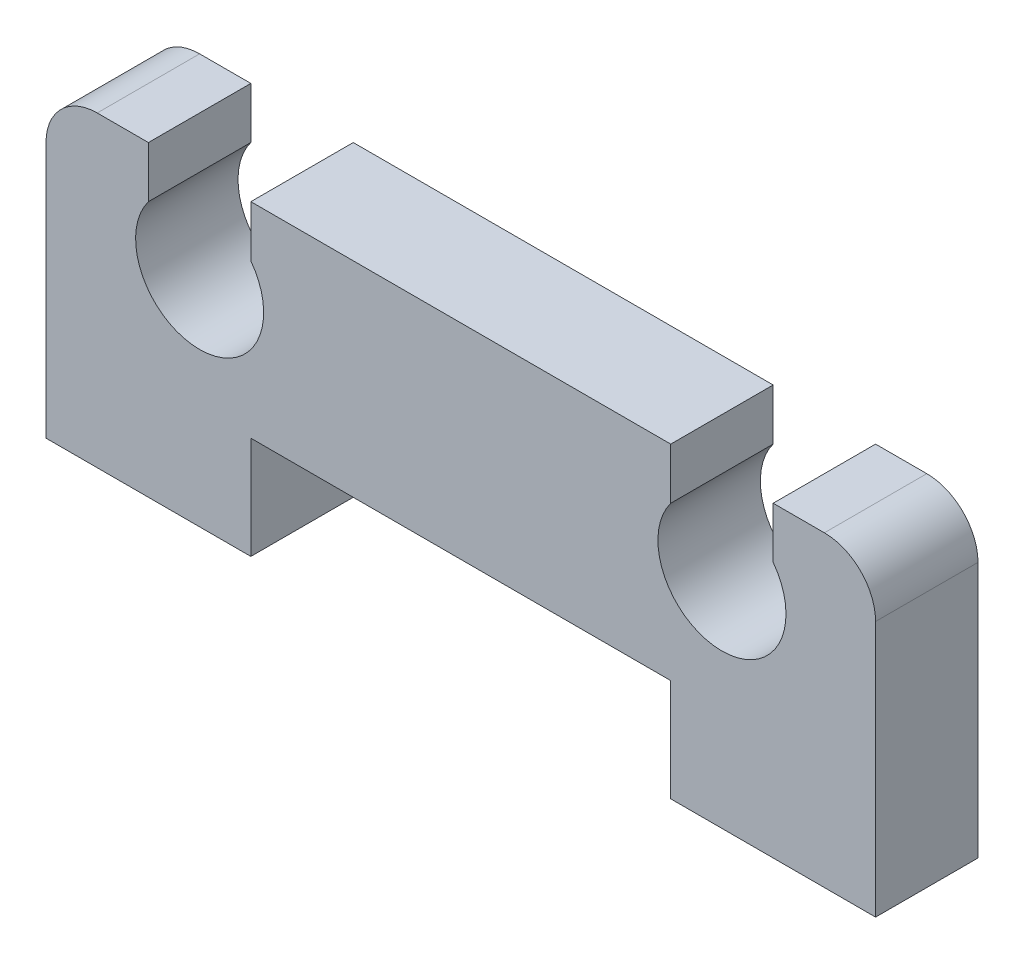
SolidWorks part; units mm, degrees
ref_plane "Front Plane" through (0, 0, 0) normal (0, 0, 1) x (1, 0, 0)
ref_plane "Top Plane" through (0, 0, 0) normal (0, 1, 0) x (1, 0, 0)
ref_plane "Right Plane" through (0, 0, 0) normal (1, 0, 0) x (0, 0, -1)
sketch "Sketch1" plane through (0, 0, 0) normal (0, 0, 1) x (1, 0, 0)
  line L0 (4, 6) -> (12.2, 6)
  line L1 (4, 2) -> (12.2, 2)
  line L2 (16.2, 0) -> (16.2, 5)
  line L3 (0, 0) -> (4, 0)
  line L4 (4, 0) -> (4, 2)
  line L5 (2, 6) -> (2, 5)
  line L6 (12.2, 6) -> (12.2, 5)
  line L7 (2, 6) -> (1, 6)
  line L8 (4, 6) -> (4, 5)
  line L9 (14.2, 6) -> (15.2, 6)
  line L10 (14.2, 6) -> (14.2, 5)
  line L11 (12.2, 0) -> (12.2, 2)
  line L12 (0, 0) -> (0, 5)
  line L13 (16.2, 0) -> (12.2, 0)
  line L14 (8.1, 2) -> (8.1, 6) construction
  arc A0 (15.2, 6) -> (16.2, 5) centre (15.2, 5) cw
  arc A1 (2, 5) -> (4, 5) centre (3, 4.25) ccw
  arc A2 (14.2, 5) -> (12.2, 5) centre (13.2, 4.25) cw
  arc A3 (1, 6) -> (0, 5) centre (1, 5) ccw
  dimension "D1" = 1.25
  dimension "D2" = 1
  dimension "D3" = 3
  dimension "D4" = 2
  dimension "D5" = 8.1
extrude "Boss-Extrude1" add sketch "Sketch1" along normal blind 2
equation "\"D5@Sketch1\"= \"fingerWidth@parametersSketch@prostheticParameters.SLDPRT\" / 2"
